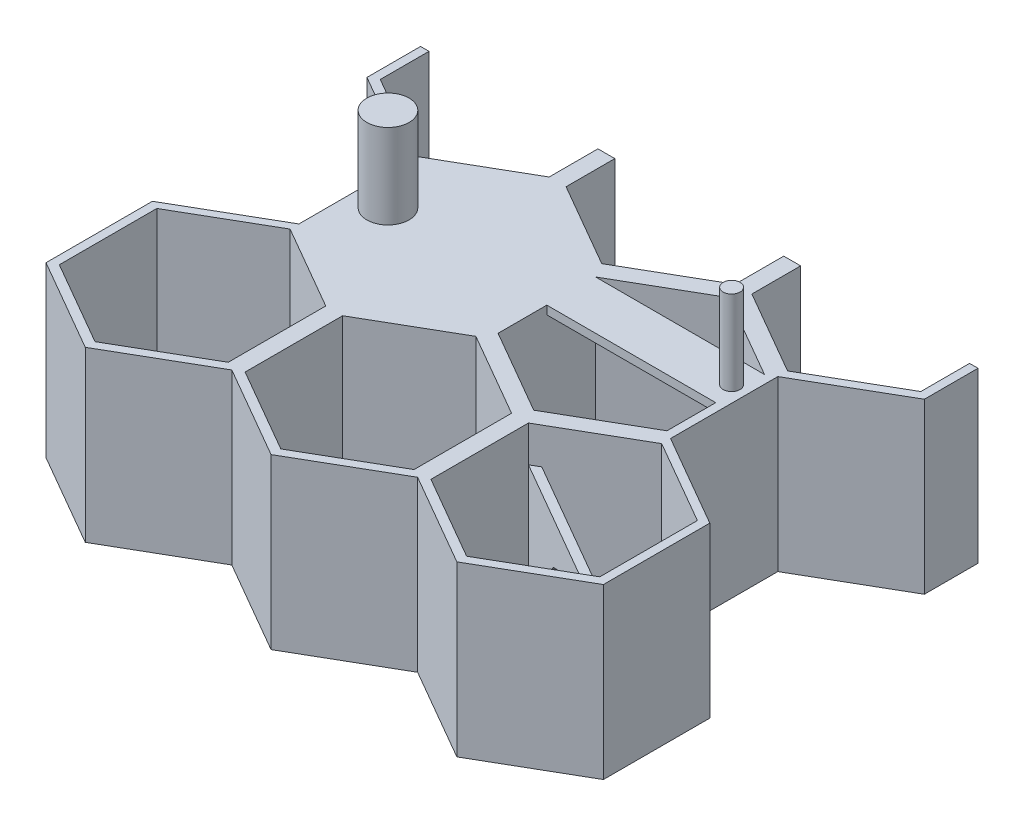
SolidWorks part; units mm, degrees
ref_plane "Front Plane" through (0, 0, 0) normal (0, 0, 1) x (1, 0, 0)
ref_plane "Top Plane" through (0, 0, 0) normal (0, 1, 0) x (1, 0, 0)
ref_plane "Right Plane" through (0, 0, 0) normal (1, 0, 0) x (0, 0, -1)
sketch "Sketch1" plane through (0, 0, 0) normal (0, 1, 0) x (1, 0, 0)
  line L0 (22, 11.547) -> (12, 5.7735)
  line L1 (0, 11.547) -> (-10, 5.7735)
  line L2 (-10, 5.7735) -> (-10, -5.7735)
  line L3 (-10, -5.7735) -> (0, -11.547)
  line L4 (0, -11.547) -> (10, -5.7735)
  line L5 (10, -5.7735) -> (10, 5.7735)
  line L6 (10, 5.7735) -> (0, 11.547)
  line L7 (11, -30.5996) -> (21, -24.8261)
  line L8 (21, -24.8261) -> (21, -13.2791)
  line L9 (21, -13.2791) -> (11, -7.5056)
  line L10 (11, -7.5056) -> (1, -13.2791)
  line L11 (1, -13.2791) -> (1, -24.8261)
  line L12 (1, -24.8261) -> (11, -30.5996)
  line L13 (12, 5.7735) -> (12, -5.7735)
  line L14 (12, -5.7735) -> (22, -11.547)
  line L15 (22, -11.547) -> (32, -5.7735)
  line L16 (32, -5.7735) -> (32, 5.7735)
  line L17 (32, 5.7735) -> (22, 11.547)
  line L18 (33, -30.5996) -> (43, -24.8261)
  line L19 (43, -24.8261) -> (43, -13.2791)
  line L20 (43, -13.2791) -> (33, -7.5056)
  line L21 (33, -7.5056) -> (23, -13.2791)
  line L22 (23, -13.2791) -> (23, -24.8261)
  line L23 (23, -24.8261) -> (33, -30.5996)
  line L24 (44, 11.547) -> (34, 5.7735)
  line L25 (34, 5.7735) -> (34, -5.7735)
  line L26 (34, -5.7735) -> (44, -11.547)
  line L27 (44, -11.547) -> (54, -5.7735)
  line L28 (54, -5.7735) -> (54, 5.7735)
  line L29 (54, 5.7735) -> (44, 11.547)
  line L30 (55, -30.5996) -> (65, -24.8261)
  line L31 (65, -24.8261) -> (65, -13.2791)
  line L32 (65, -13.2791) -> (55, -7.5056)
  line L33 (55, -7.5056) -> (45, -13.2791)
  line L34 (45, -13.2791) -> (45, -24.8261)
  line L35 (45, -24.8261) -> (55, -30.5996)
  line L36 (22, 49.547) -> (12, 43.7735)
  line L37 (12, 43.7735) -> (12, 32.2265)
  line L38 (12, 32.2265) -> (22, 26.453)
  line L39 (22, 26.453) -> (32, 32.2265)
  line L40 (32, 32.2265) -> (32, 43.7735)
  line L41 (32, 43.7735) -> (22, 49.547)
  line L42 (33, 7.4004) -> (43, 13.1739)
  line L43 (43, 13.1739) -> (43, 24.7209)
  line L44 (43, 24.7209) -> (33, 30.4944)
  line L45 (33, 30.4944) -> (23, 24.7209)
  line L46 (23, 24.7209) -> (23, 13.1739)
  line L47 (23, 13.1739) -> (33, 7.4004)
  line L48 (44, 49.547) -> (34, 43.7735)
  line L49 (34, 43.7735) -> (34, 32.2265)
  line L50 (34, 32.2265) -> (44, 26.453)
  line L51 (44, 26.453) -> (54, 32.2265)
  line L52 (54, 32.2265) -> (54, 43.7735)
  line L53 (54, 43.7735) -> (44, 49.547)
  line L54 (55, 7.4004) -> (65, 13.1739)
  line L55 (65, 13.1739) -> (65, 24.7209)
  line L56 (65, 24.7209) -> (55, 30.4944)
  line L57 (55, 30.4944) -> (45, 24.7209)
  line L58 (45, 24.7209) -> (45, 13.1739)
  line L59 (45, 13.1739) -> (55, 7.4004)
  line L60 (0, 49.547) -> (-10, 43.7735)
  line L61 (-10, 43.7735) -> (-10, 32.2265)
  line L62 (-10, 32.2265) -> (0, 26.453)
  line L63 (0, 26.453) -> (10, 32.2265)
  line L64 (10, 32.2265) -> (10, 43.7735)
  line L65 (10, 43.7735) -> (0, 49.547)
  line L66 (11, 7.4004) -> (21, 13.1739)
  line L67 (21, 13.1739) -> (21, 24.7209)
  line L68 (21, 24.7209) -> (11, 30.4944)
  line L69 (11, 30.4944) -> (1, 24.7209)
  line L70 (1, 24.7209) -> (1, 13.1739)
  line L71 (1, 13.1739) -> (11, 7.4004)
  line L72 (66, 11.547) -> (56, 5.7735)
  line L74 (11, -19.0526) -> (11, 38)
  line L75 (11, 38) -> (66, 38)
  line L77 (56, 5.7735) -> (56, -5.7735)
  line L78 (56, -5.7735) -> (66, -11.547)
  line L79 (66, -11.547) -> (76, -5.7735)
  line L80 (76, -5.7735) -> (76, 5.7735)
  line L81 (76, 5.7735) -> (66, 11.547)
  line L82 (77, -30.5996) -> (87, -24.8261)
  line L83 (87, -24.8261) -> (87, -13.2791)
  line L84 (87, -13.2791) -> (77, -7.5056)
  line L85 (77, -7.5056) -> (67, -13.2791)
  line L86 (67, -13.2791) -> (67, -24.8261)
  line L87 (67, -24.8261) -> (77, -30.5996)
  line L88 (66, 49.547) -> (56, 43.7735)
  line L89 (56, 43.7735) -> (56, 32.2265)
  line L90 (56, 32.2265) -> (66, 26.453)
  line L91 (66, 26.453) -> (76, 32.2265)
  line L92 (76, 32.2265) -> (76, 43.7735)
  line L93 (76, 43.7735) -> (66, 49.547)
  line L94 (77, 7.4004) -> (87, 13.1739)
  line L95 (87, 13.1739) -> (87, 24.7209)
  line L96 (87, 24.7209) -> (77, 30.4944)
  line L97 (77, 30.4944) -> (67, 24.7209)
  line L98 (67, 24.7209) -> (67, 13.1739)
  line L99 (67, 13.1739) -> (77, 7.4004)
  line L100 (11, -19.0526) -> (77, -19.0526)
  line L101 (77, -19.0526) -> (77, 38)
  line L102 (77, 38) -> (66, 38)
  circle A0 centre (0, 0) radius 10 construction
  circle A1 centre (11, -19.0526) radius 10 construction
  circle A2 centre (22, 0) radius 10 construction
  circle A3 centre (33, -19.0526) radius 10 construction
  circle A4 centre (44, 0) radius 10 construction
  circle A5 centre (55, -19.0526) radius 10 construction
  circle A6 centre (22, 38) radius 10 construction
  circle A7 centre (33, 18.9474) radius 10 construction
  circle A8 centre (44, 38) radius 10 construction
  circle A9 centre (55, 18.9474) radius 10 construction
  circle A10 centre (0, 38) radius 10 construction
  circle A11 centre (11, 18.9474) radius 10 construction
  circle A12 centre (66, 0) radius 10 construction
  circle A13 centre (77, -19.0526) radius 10 construction
  circle A14 centre (66, 38) radius 10 construction
  circle A15 centre (77, 18.9474) radius 10 construction
  dimension "D1" = 20
  dimension "D2" = 2
  dimension "D3" = 1
  dimension "D4" = 4
  dimension "D5" = 2
extrude "Boss-Extrude2" add sketch "Sketch1" along normal blind 20
sketch "Sketch2" plane through (0, 20, 0) normal (0, 1, 0) x (1, 0, 0)
  line L0 (11, 6.2457) -> (22, 12.5966)
  line L1 (11, -7.5056) -> (11, 7.4004) construction
  line L2 (22, 12.5966) -> (22, 25.2983)
  line L3 (22, 25.2983) -> (11, 31.6491)
  line L4 (11, 30.4944) -> (11, 38) construction
  line L5 (11, -6.3509) -> (22, -12.7017)
  line L6 (22, -12.7017) -> (22, -19.0526)
  line L9 (21, -13.2791) -> (11, -7.5056) construction
  line L11 (11, 7.4004) -> (21, 13.1739) construction
  line L13 (21, 24.7209) -> (11, 30.4944) construction
  line L14 (11, 6.2457) -> (11, -6.3509)
  line L15 (11, 31.6491) -> (2.2959, -19.0526)
  line L16 (2.2959, -19.0526) -> (22, -19.0526)
  line L17 (21, -19.0526) -> (23, -19.0526) construction
  line L19 (44, 26.453) -> (44, -11.547) construction
  line L20 (77, 31.6491) -> (85.7041, -19.0526)
  line L21 (66, 25.2983) -> (77, 31.6491)
  line L22 (66, 12.5966) -> (66, 25.2983)
  line L23 (77, 6.2457) -> (66, 12.5966)
  line L24 (77, 6.2457) -> (77, -6.3509)
  line L25 (77, -6.3509) -> (66, -12.7017)
  line L26 (66, -12.7017) -> (66, -19.0526)
  line L27 (85.7041, -19.0526) -> (66, -19.0526)
  point P18 (22, -19.0526)
  dimension "D1" = 1
  dimension "D2" = 1
  dimension "D3" = 1
extrude "Cut-Extrude1" cut sketch "Sketch2" against normal through all
sketch "Sketch3" plane through (0, 20, 0) normal (0, 1, 0) x (1, 0, 0)
  line L0 (22, -12.7017) -> (33, -6.3509)
  line L1 (33, -6.3509) -> (44, -12.7017)
  line L2 (44, -12.7017) -> (55, -6.3509)
  line L3 (55, -6.3509) -> (66, -12.7017)
  line L4 (33, -7.5056) -> (23, -13.2791) construction
  line L5 (43, -13.2791) -> (33, -7.5056) construction
  line L6 (65, -13.2791) -> (55, -7.5056) construction
  line L7 (44, -11.547) -> (54, -5.7735) construction
  line L8 (22, -12.7017) -> (22, -19.0526)
  line L9 (22, -19.0526) -> (66, -19.0526)
  line L10 (66, -19.0526) -> (66, -12.7017)
  dimension "D1" = 1
  dimension "D2" = 1
extrude "Cut-Extrude2" cut sketch "Sketch3" against normal through all
sketch "Sketch4" plane through (0, 20, 0) normal (0, 1, 0) x (1, 0, 0)
  line L0 (65, 13.1739) -> (65, 24.7209) construction
  line L1 (33, 7.4004) -> (43, 13.1739)
  line L2 (43, 13.1739) -> (43, 24.7209)
  line L3 (43, 24.7209) -> (33, 30.4944)
  line L4 (33, 30.4944) -> (23, 24.7209)
  line L5 (23, 24.7209) -> (23, 13.1739)
  line L6 (23, 13.1739) -> (33, 7.4004)
  line L7 (45, 24.7209) -> (65, 24.7209)
  line L8 (45, 24.7209) -> (45, 18.9474)
  line L9 (45, 18.9474) -> (65, 18.9474)
  line L10 (65, 24.7209) -> (65, 18.9474)
  circle A0 centre (33, 18.9474) radius 10 construction
extrude "Boss-Extrude3" add sketch "Sketch4" against normal blind 1
ref_plane "Plane1" through (16.5, 0, -28.5788) normal (0.5, 0, -0.866) x (-0.866, 0, -0.5)
sketch "Sketch5" plane through (16.5, 0, -28.5788) normal (0.5, 0, -0.866) x (-0.866, 0, -0.5)
  line L0 (-45.6107, 0) -> (-45.6107, 15.7105)
  line L1 (-45.6107, 15.7105) -> (-60.3975, 15.7105)
  line L3 (-45.6107, 0) -> (-49.1841, 6.1894)
  line L4 (-49.1841, 6.1894) -> (-53.7453, 10.7506)
  line L5 (-53.7453, 10.7506) -> (-58.5424, 12.9875)
  line L6 (-58.5424, 12.9875) -> (-68.7047, 15.7105)
  line L7 (-68.7047, 15.7105) -> (-60.3975, 15.7105)
  line L8 (-68.7047, 20) -> (-68.7047, 0) construction
  dimension "D1" = 30
  dimension "D2" = 45
  dimension "D3" = 65
  dimension "D4" = 75
extrude "Boss-Extrude6" add sketch "Sketch5" along normal blind 1
sketch "Sketch6" plane through (0, 20, 0) normal (0, 1, 0) x (1, 0, 0)
  circle A0 centre (64.0998, 21.7264) radius 1
  circle A1 centre (25.6137, 19.5242) radius 2.5
  point P4 (64.0998, 21.7264)
  point P5 (25.6137, 19.5242)
  dimension "D1" = 2
  dimension "D2" = 5
extrude "Boss-Extrude7" add sketch "Sketch6" along normal blind 10
equation "\"parois_t\"= 2mm"
equation "\"panneau_t\"= 20mm"
equation "\"entreplat_interne\"= 20mm"
equation "\"D1@Sketch1\"=\"entreplat_interne\""
equation "\"D2@Sketch1\"=\"parois_t\""
equation "\"D2@Sketch3\"=\"parois_t\"/2"
